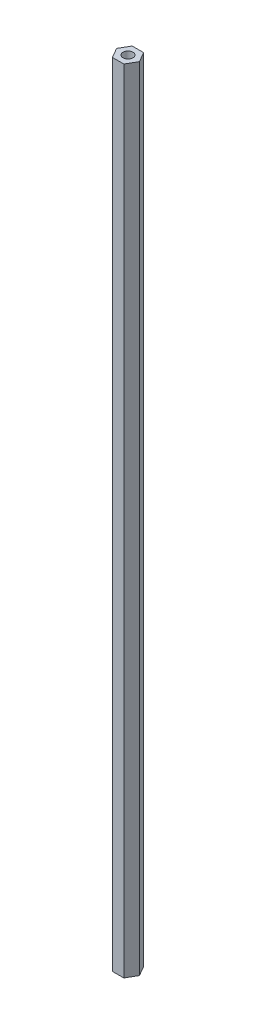
SolidWorks part; units mm, degrees
material "6061-T6 (SS)"
ref_plane "Front Plane" through (0, 0, 0) normal (0, 0, 1) x (1, 0, 0)
ref_plane "Top Plane" through (0, 0, 0) normal (0, 1, 0) x (1, 0, 0)
ref_plane "Right Plane" through (0, 0, 0) normal (1, 0, 0) x (0, 0, -1)
sketch "Sketch1" plane through (0, 0, 0) normal (0, 1, 0) x (1, 0, 0)
  line L1 (3.6662, -6.35) -> (7.3323, 0)
  line L2 (7.3323, 0) -> (3.6662, 6.35)
  line L3 (3.6662, 6.35) -> (-3.6662, 6.35)
  line L4 (-3.6662, 6.35) -> (-7.3323, 0)
  line L5 (-7.3323, 0) -> (-3.6662, -6.35)
  line L6 (-3.6662, -6.35) -> (3.6662, -6.35)
  circle A0 centre (0, 0) radius 6.35 construction
  circle A1 centre (0, 0) radius 3.175
  dimension "D2" = 6.35
  dimension "D1" = 12.7
extrude "Boss-Extrude1" add sketch "Sketch1" along normal blind 508
